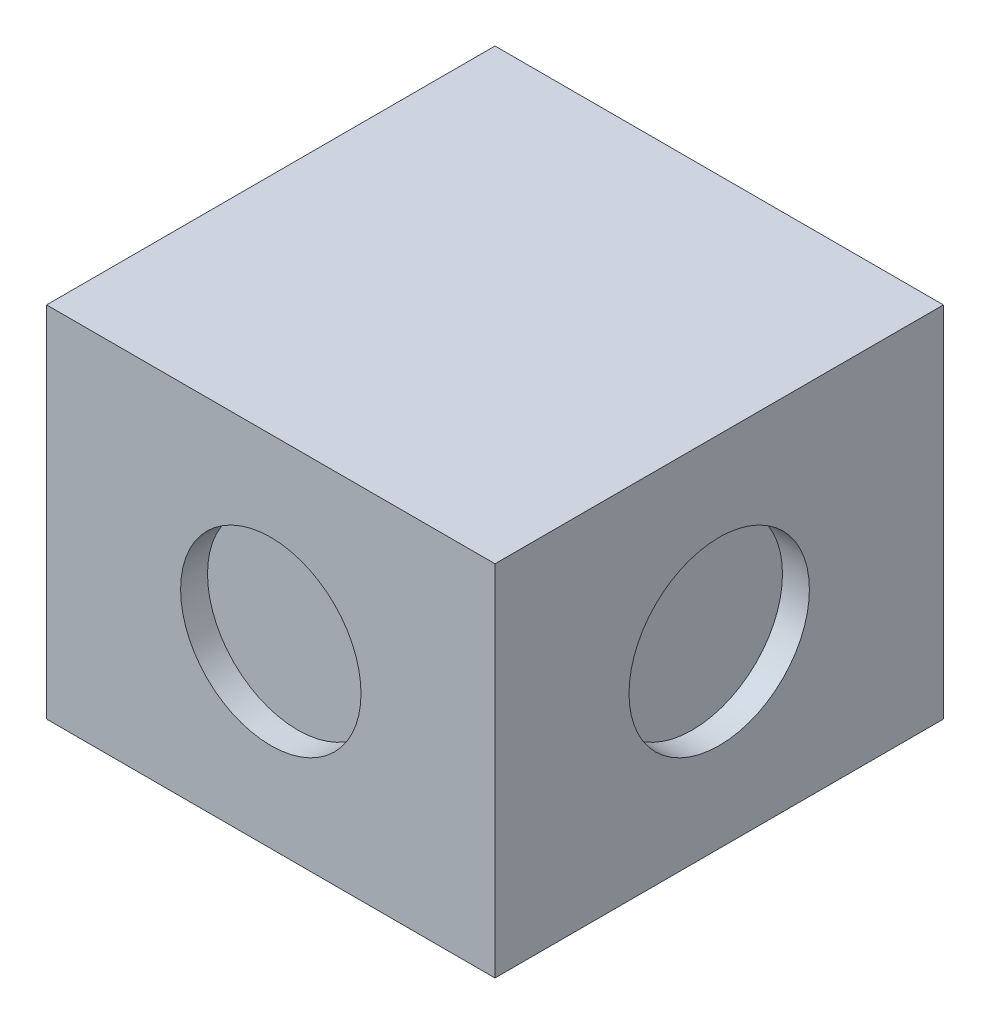
SolidWorks part; units mm, degrees
ref_plane "Front Plane" through (0, 0, 0) normal (0, 0, 1) x (1, 0, 0)
ref_plane "Top Plane" through (0, 0, 0) normal (0, 1, 0) x (1, 0, 0)
ref_plane "Right Plane" through (0, 0, 0) normal (1, 0, 0) x (0, 0, -1)
sketch "Sketch1" plane through (0, 0, 0) normal (0, 1, 0) x (1, 0, 0)
  line L1 (-25, -25) -> (25, -25)
  line L2 (-25, -25) -> (-25, 25)
  line L3 (-25, 25) -> (25, 25)
  line L4 (25, -25) -> (25, 25)
  line L5 (-25, -25) -> (25, 25) construction
  line L6 (-25, 25) -> (25, -25) construction
  point P0 (0, 0)
  dimension "D1" = 50
  dimension "D2" = 50
extrude "Boss-Extrude1" add sketch "Sketch1" along normal blind 40
sketch "Sketch2" plane through (0, 0, 0) normal (0, -1, 0) x (1, 0, 0)
  circle A0 centre (0, 0) radius 17
  dimension "D1" = 34
sketch "Sketch4" plane through (0, 0, 25) normal (0, 0, 1) x (1, 0, 0)
  line L0 (0, 20) -> (0, 40) construction
  line L1 (-25, 40) -> (25, 40) construction
  line L2 (0, 20) -> (0, 0) construction
  circle A0 centre (0, 20) radius 10.0571
  dimension "D1" = 20.1142
sketch "Sketch5" plane through (25, 0, 0) normal (1, 0, 0) x (0, 0, -1)
  line L0 (0, 20) -> (0, 40) construction
  line L1 (-25, 40) -> (25, 40) construction
  line L2 (0, 20) -> (0, 0) construction
  circle A0 centre (0, 20) radius 10.0571
  dimension "D1" = 20.1142
extrude "Cut-Extrude1" cut sketch "Sketch5" against normal blind 3
extrude "Cut-Extrude2" cut sketch "Sketch4" against normal blind 3 contours A0
extrude "Cut-Extrude3" cut sketch "Sketch2" against normal blind 3 contours A0
